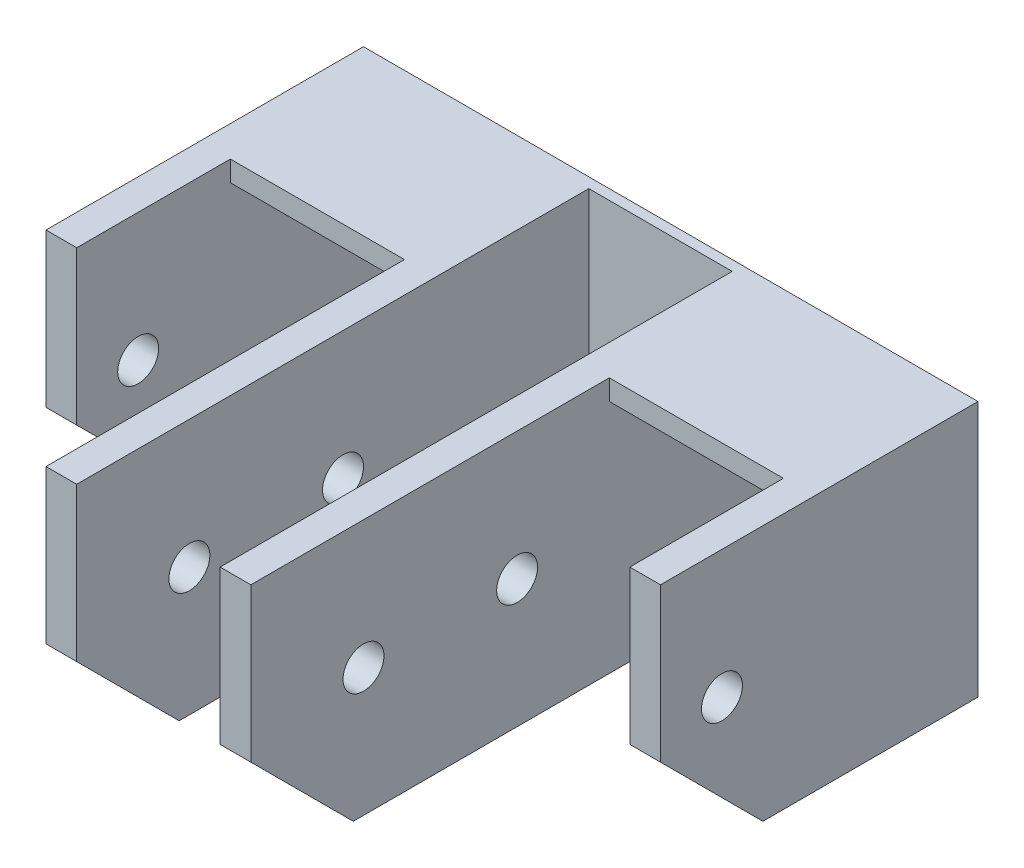
SolidWorks part; units mm, degrees
material "3.0526 (EN-AW 3004)"
ref_plane "Płaszczyzna XY" through (0, 0, 0) normal (0, 0, 1) x (1, 0, 0)
ref_plane "Płaszczyzna XZ" through (0, 0, 0) normal (0, 1, 0) x (1, 0, 0)
ref_plane "Płaszczyzna YZ" through (0, 0, 0) normal (1, 0, 0) x (0, 0, -1)
sketch "Szkic1" plane through (0, 0, 0) normal (0, 0, 1) x (1, 0, 0)
  line L1 (0, 0) -> (60, 0)
  line L2 (0, 0) -> (0, 25)
  line L3 (0, 25) -> (60, 25)
  line L4 (60, 0) -> (60, 25)
  dimension "D1" = 60
  dimension "D2" = 25
extrude "Dodanie-wyciągnięcie1" add sketch "Szkic1" along normal blind 1
sketch "Szkic3" plane through (0, 0, 1) normal (0, 0, 1) x (1, 0, 0)
  line L0 (0, 0) -> (0, 25)
  line L1 (0, 25) -> (60, 25)
  line L2 (60, 25) -> (60, 0)
  line L3 (60, 0) -> (57, 0)
  line L4 (0, 0) -> (60, 0) construction
  line L5 (57, 0) -> (57, 23)
  line L6 (57, 23) -> (40, 23)
  line L7 (40, 23) -> (40, 0)
  line L8 (40, 0) -> (37, 0)
  line L9 (37, 0) -> (37, 23)
  line L10 (37, 23) -> (23, 23)
  line L11 (23, 23) -> (23, 0)
  line L12 (23, 0) -> (20, 0)
  line L13 (20, 0) -> (20, 23)
  line L14 (20, 23) -> (3, 23)
  line L15 (3, 23) -> (3, 0)
  line L16 (3, 0) -> (0, 0)
  dimension "D1" = 2
  dimension "D2" = 17
  dimension "D3" = 3
  dimension "D4" = 3
extrude "Dodanie-wyciągnięcie2" add sketch "Szkic3" along normal blind 50
sketch "Szkic4" plane through (0, 0, 0) normal (-1, 0, 0) x (0, 0, 1)
  line L0 (40, 12.5) -> (25, 12.5) construction
  line L1 (51, 25) -> (0, 25) construction
  line L2 (0, 25) -> (0, 0) construction
  circle A0 centre (25, 12.5) radius 2
  circle A1 centre (40, 12.5) radius 2
  dimension "D1" = 4
  dimension "D2" = 12.5
  dimension "D3" = 25
  dimension "D4" = 40
extrude "Wytnij-wyciągnięcie1" cut sketch "Szkic4" against normal through all
sketch "Szkic5" plane through (0, 0, 51) normal (0, 0, 1) x (1, 0, 0)
  line L0 (60, 25) -> (0, 25) construction
  line L1 (57, 23) -> (40, 23)
  line L2 (57, 23) -> (57, 25)
  line L3 (57, 25) -> (40, 25)
  line L4 (40, 23) -> (40, 25)
  line L5 (40, 0) -> (40, 23) construction
  line L6 (3, 0) -> (3, 23) construction
  line L7 (20, 23) -> (3, 23)
  line L8 (20, 23) -> (20, 25)
  line L9 (20, 25) -> (3, 25)
  line L10 (3, 23) -> (3, 25)
extrude "Wytnij-wyciągnięcie2" cut sketch "Szkic5" against normal blind 35
sketch "Szkic6" plane through (0, 0, 0) normal (-1, 0, 0) x (0, 0, 1)
  line L0 (51, 0) -> (0, 0) construction
  line L1 (51, 25) -> (31, 25)
  line L2 (51, 25) -> (51, 0)
  line L3 (51, 0) -> (31, 0)
  line L4 (31, 25) -> (31, 0)
  dimension "D1" = 20
extrude "Wytnij-wyciągnięcie3" cut sketch "Szkic6" against normal blind 3
sketch "Szkic7" plane through (60, 0, 0) normal (1, 0, 0) x (0, 0, -1)
  line L0 (-51, 0) -> (0, 0) construction
  line L1 (-51, 25) -> (-31, 25)
  line L2 (-51, 25) -> (-51, 0)
  line L3 (-51, 0) -> (-31, 0)
  line L4 (-31, 25) -> (-31, 0)
  dimension "D1" = 20
extrude "Wytnij-wyciągnięcie4" cut sketch "Szkic7" against normal blind 3
chamfer "Sfazowanie1" distance 10 angle 45 4 edges at (58.5, 0, 31) (1.5, 0, 31) (38.5, 0, 51) (21.5, 0, 51)
sketch "Szkic8" plane through (0, 0, 1) normal (0, 0, 1) x (1, 0, 0)
  line L0 (3, 23) -> (20, 0) construction
  line L1 (20, 0) -> (20, 23) construction
  line L2 (20, 23) -> (3, 0) construction
  line L3 (3, 0) -> (23, 0) construction
  line L4 (23, 0) -> (40, 23) construction
  line L5 (40, 23) -> (40, 0) construction
  line L6 (40, 0) -> (23, 23) construction
  line L7 (23, 23) -> (40, 23) construction
  line L8 (40, 23) -> (57, 0) construction
  line L9 (57, 0) -> (57, 23) construction
  line L10 (57, 23) -> (40, 0) construction
  circle A0 centre (11.5, 11.5) radius 2.5
  circle A2 centre (48.5, 11.5) radius 2.5
  dimension "D1" = 5
extrude "Wytnij-wyciągnięcie5" cut sketch "Szkic8" against normal blind 3
sketch "Szkic9" plane through (0, 0, 51) normal (0, 0, 1) x (1, 0, 0)
  line L1 (23, 23) -> (37, 23)
  line L2 (23, 23) -> (23, 25)
  line L3 (23, 25) -> (37, 25)
  line L4 (37, 23) -> (37, 25)
  line L5 (37, 23) -> (37, 10) construction
  line L6 (40, 25) -> (20, 25) construction
extrude "Wytnij-wyciągnięcie6" cut sketch "Szkic9" against normal blind 50
